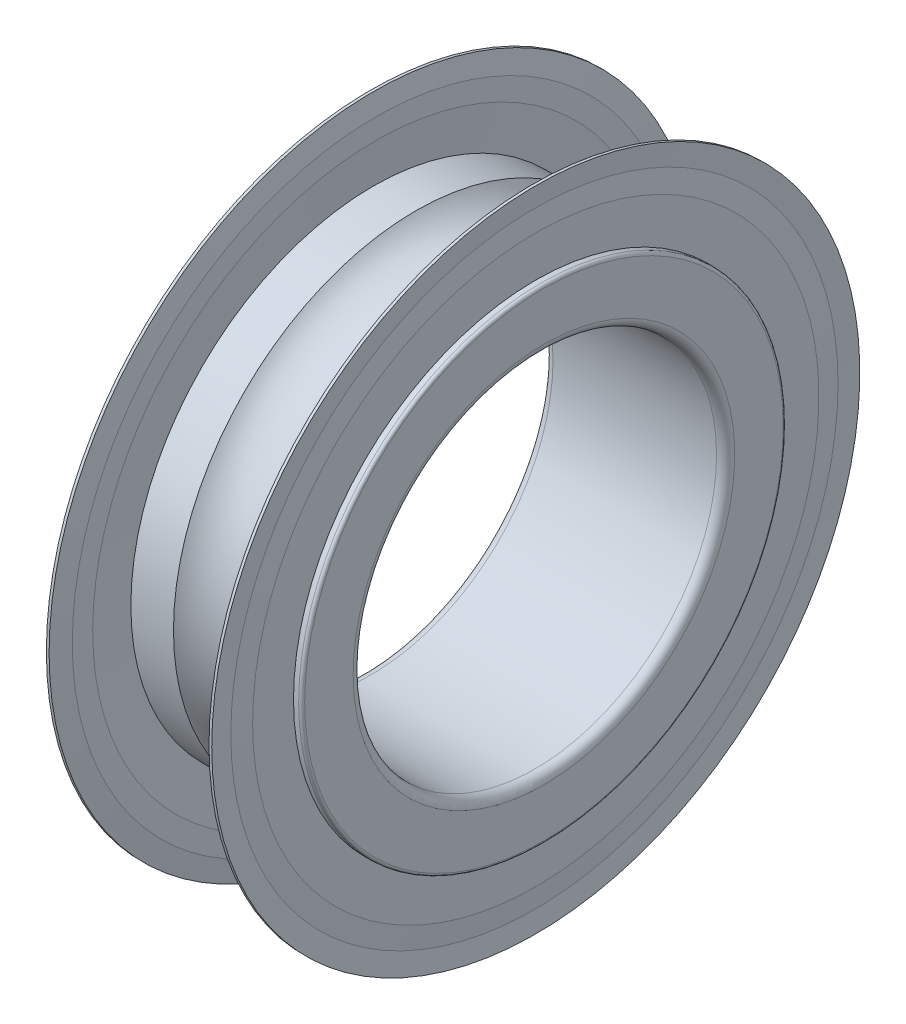
SolidWorks part; units mm, degrees
ref_plane "Front Plane" through (0, 0, 0) normal (0, 0, 1) x (1, 0, 0)
ref_plane "Top Plane" through (0, 0, 0) normal (0, 1, 0) x (1, 0, 0)
ref_plane "Right Plane" through (0, 0, 0) normal (1, 0, 0) x (0, 0, -1)
ref_plane "Plane1" through (0, 0, 0) normal (0, 0, 1) x (1, 0, 0)
sketch "Sketch1" plane through (0, 0, 0) normal (0, 0, 1) x (1, 0, 0)
  line L0 (0, 7.9) -> (0, 6.3)
  line L1 (0.3, 6) -> (5.7, 6)
  line L2 (6, 6.3) -> (6, 7.9)
  line L3 (5.9, 8) -> (4.2329, 8)
  line L4 (1.7671, 8) -> (0.1, 8)
  line L5 (50, 0) -> (-50, 0) construction
  arc A0 (0, 6.3) -> (0.3, 6) centre (0.3, 6.3) ccw
  arc A1 (5.7, 6) -> (6, 6.3) centre (5.7, 6.3) ccw
  arc A2 (6, 7.9) -> (5.9, 8) centre (5.9, 7.9) ccw
  arc A3 (4.2329, 8) -> (1.7671, 8) centre (3, 9) cw
  arc A4 (0.1, 8) -> (0, 7.9) centre (0.1, 7.9) ccw
revolve "Revolve1" add sketch "Sketch1" angle 360 about L5
ref_plane "Plane2" through (0, 0, 0) normal (0, 0, 1) x (1, 0, 0)
sketch "Sketch2" plane through (0, 0, 0) normal (0, 0, 1) x (1, 0, 0)
  line L0 (0.27, 10.7) -> (0.315, 10.025)
  line L1 (0.315, 10.025) -> (0.27, 9.35)
  line L2 (0.27, 9.35) -> (0.27, 8)
  line L3 (0.27, 8) -> (0.36, 8)
  line L4 (0.36, 8) -> (0.45, 9.35)
  line L5 (0.45, 9.35) -> (0.45, 10.025)
  line L6 (0.45, 10.025) -> (0.36, 10.7)
  line L7 (0.36, 10.7) -> (0.27, 10.7)
  line L8 (50, 0) -> (-50, 0) construction
revolve "Revolve2" add sketch "Sketch2" angle 360 about L8
ref_plane "Plane3" through (0, 0, 0) normal (0, 0, 1) x (1, 0, 0)
sketch "Sketch3" plane through (0, 0, 0) normal (0, 0, 1) x (1, 0, 0)
  line L0 (5.55, 10.025) -> (5.55, 9.35)
  line L1 (5.55, 9.35) -> (5.64, 8)
  line L2 (5.64, 8) -> (5.73, 8)
  line L3 (5.73, 8) -> (5.73, 9.35)
  line L4 (5.73, 9.35) -> (5.685, 10.025)
  line L5 (5.685, 10.025) -> (5.73, 10.7)
  line L6 (5.73, 10.7) -> (5.64, 10.7)
  line L7 (5.64, 10.7) -> (5.55, 10.025)
  line L8 (50, 0) -> (-50, 0) construction
revolve "Revolve3" add sketch "Sketch3" angle 360 about L8
